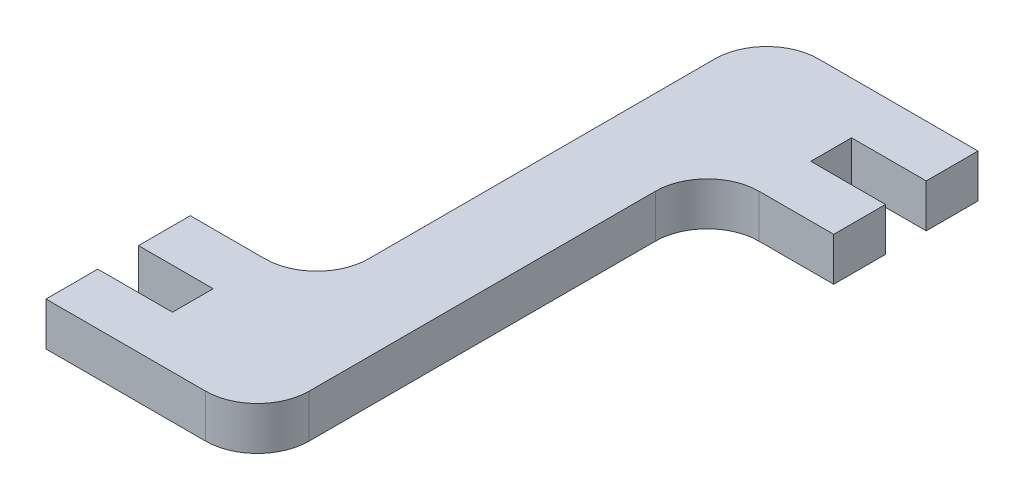
SolidWorks part; units mm, degrees
material "Balsa"
ref_plane "Alzado" through (0, 0, 0) normal (0, 0, 1) x (1, 0, 0)
ref_plane "Planta" through (0, 0, 0) normal (0, 1, 0) x (1, 0, 0)
ref_plane "Vista lateral" through (0, 0, 0) normal (1, 0, 0) x (0, 0, -1)
sketch "Croquis1" plane through (0, 0, 0) normal (0, 1, 0) x (1, 0, 0)
  line L0 (0, 0) -> (18.8, 0)
  line L1 (0, 0) -> (0, 6.1)
  line L2 (0, 6.1) -> (8.8, 6.1)
  line L3 (8.8, 6.1) -> (8.8, 10.9)
  line L4 (8.8, 10.9) -> (0, 10.9)
  line L5 (0, 10.9) -> (0, 17)
  line L6 (0, 17) -> (8.8, 17)
  line L7 (14.9, 23.1) -> (14.9, 63.9)
  line L8 (24.9, 6.1) -> (24.9, 46.9)
  line L9 (21, 70) -> (39.8, 70)
  line L10 (39.8, 70) -> (39.8, 63.9)
  line L11 (39.8, 63.9) -> (31, 63.9)
  line L12 (31, 63.9) -> (31, 59.1)
  line L13 (31, 59.1) -> (39.8, 59.1)
  line L14 (39.8, 59.1) -> (39.8, 53)
  line L15 (39.8, 53) -> (31, 53)
  arc A0 (18.8, 0) -> (24.9, 6.1) centre (18.8, 6.1) ccw
  arc A1 (8.8, 17) -> (14.9, 23.1) centre (8.8, 23.1) ccw
  arc A2 (24.9, 46.9) -> (31, 53) centre (31, 46.9) cw
  arc A3 (14.9, 63.9) -> (21, 70) centre (21, 63.9) cw
extrude "Saliente-Extruir1" add sketch "Croquis1" along normal blind 5.1
equation "\"Ranura\" =4.8"
equation "\"D2@Croquis1\"=\"Ranura\""
equation "\"Material\"=5.1"
equation "\"D4@Croquis1\"=\"D5@Croquis1\"/10+3"
equation "\"D3@Croquis1\"=\"D2@Croquis1\"+4"
equation "\"D1@Saliente-Extruir1\"=\"Material\""
equation "\"Altura\"= 70"
equation "\"D5@Croquis1\"=\"Altura\""
